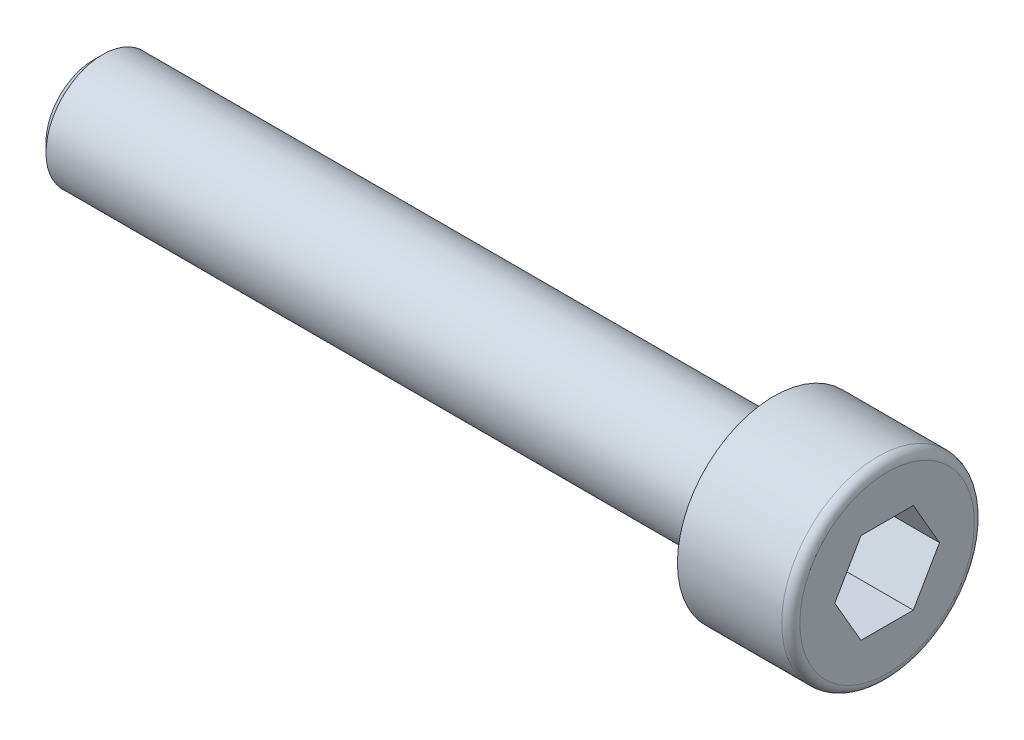
SolidWorks part; units mm, degrees
material "1.0503 (C45)"
ref_plane "Płaszczyzna XY" through (0, 0, 0) normal (0, 0, 1) x (1, 0, 0)
ref_plane "Płaszczyzna XZ" through (0, 0, 0) normal (0, 1, 0) x (1, 0, 0)
ref_plane "Płaszczyzna YZ" through (0, 0, 0) normal (1, 0, 0) x (0, 0, -1)
sketch "Szkic1" plane through (0, 0, 0) normal (0, 0, 1) x (1, 0, 0)
  line L0 (-123.1589, 0) -> (95.9851, 0) construction
  line L1 (0, 0) -> (0, 4.25)
  line L2 (0, 4.25) -> (-5, 4.25)
  line L3 (-5, 4.25) -> (-5, 2.5)
  line L4 (-5, 2.5) -> (-35, 2.5)
  line L5 (-35, 2.5) -> (-35, 0)
  line L6 (0, 0) -> (-35, 0)
  dimension "Dk" = 8.5
  dimension "d" = 5
  dimension "b" = 30
  dimension "k" = 5
revolve "Obrót1" add sketch "Szkic1" angle 360 about L0
chamfer "Sfazowanie1" distance 0.4 1 edges at (-35, 0, 2.5)
fillet "Zaokrąglenie1" radius 0.4 1 edges at (0, 0, 4.25)
sketch "Szkic2" plane through (0, 0, 0) normal (1, 0, 0) x (0, 0, -1)
  line L1 (2.3094, 0) -> (1.1547, 2)
  line L2 (1.1547, 2) -> (-1.1547, 2)
  line L3 (-1.1547, 2) -> (-2.3094, 0)
  line L4 (-2.3094, 0) -> (-1.1547, -2)
  line L5 (-1.1547, -2) -> (1.1547, -2)
  line L6 (1.1547, -2) -> (2.3094, 0)
  circle A0 centre (0, 0) radius 2 construction
  dimension "s" = 4
extrude "Wytnij-wyciągnięcie1" cut sketch "Szkic2" against normal offset from surface (4 mm away) 1 up to face at (-5, 0, 2.5)
